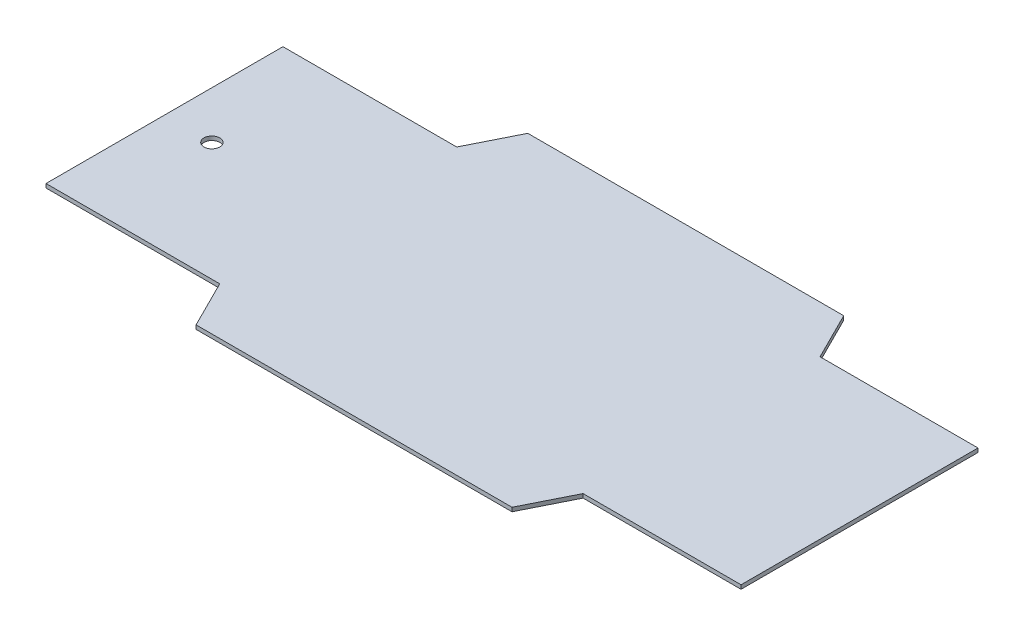
SolidWorks part; units mm, degrees
ref_plane "Front Plane" through (0, 0, 0) normal (0, 0, 1) x (1, 0, 0)
ref_plane "Top Plane" through (0, 0, 0) normal (0, 1, 0) x (1, 0, 0)
ref_plane "Right Plane" through (0, 0, 0) normal (1, 0, 0) x (0, 0, -1)
sketch "Sketch3" plane through (0, 0, 0) normal (0, 1, 0) x (1, 0, 0)
  line L0 (-279.4, 95.25) -> (-139.7, 95.25)
  line L1 (-279.4, -133.35) -> (279.4, -133.35) construction
  line L2 (-279.4, -133.35) -> (-279.4, 133.35) construction
  line L3 (-279.4, 133.35) -> (279.4, 133.35) construction
  line L4 (279.4, -133.35) -> (279.4, 133.35) construction
  line L5 (-279.4, -133.35) -> (279.4, 133.35) construction
  line L6 (-279.4, 133.35) -> (279.4, -133.35) construction
  line L7 (-279.4, -95.25) -> (279.4, -95.25) construction
  line L8 (-279.4, -95.25) -> (-279.4, 95.25) construction
  line L9 (-279.4, 95.25) -> (279.4, 95.25) construction
  line L10 (279.4, -95.25) -> (279.4, 95.25) construction
  line L13 (-139.7, 95.25) -> (-120.65, 133.35)
  line L14 (-120.65, 133.35) -> (133.35, 133.35)
  line L15 (133.35, 133.35) -> (152.4, 95.25)
  line L16 (152.4, 95.25) -> (279.4, 95.25)
  line L17 (-279.4, 95.25) -> (-279.4, -95.25)
  line L18 (279.4, 95.25) -> (279.4, -95.25)
  line L19 (-279.4, 0) -> (279.4, 0) construction
  line L20 (152.4, -95.25) -> (279.4, -95.25)
  line L21 (133.35, -133.35) -> (152.4, -95.25)
  line L22 (-120.65, -133.35) -> (133.35, -133.35)
  line L23 (-139.7, -95.25) -> (-120.65, -133.35)
  line L24 (-279.4, -95.25) -> (-139.7, -95.25)
  point P0 (0, 0)
  point P6 (0, 0)
  dimension "D1" = 266.7
  dimension "D2" = 558.8
  dimension "D3" = 190.5
  dimension "D4" = 127
  dimension "D5" = 139.7
  dimension "D6" = 254
extrude "Boss-Extrude1" add sketch "Sketch3" along normal mid plane 3.175
sketch "Sketch5" plane through (0, -1.5875, 0) normal (0, -1, 0) x (1, 0, 0)
  line L0 (-202.3532, 0) -> (279.4, 0) construction
  line L1 (-63.5, 25.4) -> (76.2, 25.4)
  line L2 (-63.5, 25.4) -> (-63.5, 88.9)
  line L3 (-63.5, 88.9) -> (76.2, 88.9)
  line L4 (76.2, 25.4) -> (76.2, 88.9)
  line L5 (-63.5, 25.4) -> (76.2, 88.9) construction
  line L6 (-63.5, 88.9) -> (76.2, 25.4) construction
  line L7 (279.4, 95.25) -> (279.4, -95.25) construction
  line L8 (-120.65, 133.35) -> (133.35, 133.35) construction
  line L9 (-120.65, 133.35) -> (133.35, 133.35) construction
  line L10 (6.35, 133.35) -> (6.35, 88.9) construction
  line L11 (-63.5, -88.9) -> (76.2, -88.9)
  line L12 (76.2, -25.4) -> (76.2, -88.9)
  line L13 (-63.5, -25.4) -> (76.2, -25.4)
  line L14 (-63.5, -25.4) -> (-63.5, -88.9)
  point P4 (6.35, 57.15)
  dimension "D1" = 63.5
  dimension "D2" = 139.7
  dimension "D3" = 44.45
sketch "Sketch6" plane through (0, 1.5875, 0) normal (0, 1, 0) x (1, 0, 0)
  line L0 (-279.4, 95.25) -> (-139.7, 95.25) construction
  line L1 (-120.65, 133.35) -> (-139.7, 95.25) construction
  line L2 (-139.7, 95.25) -> (-279.4, 95.25) construction
  line L3 (-139.7, 95.25) -> (-120.65, 133.35) construction
  line L4 (-120.65, 133.35) -> (133.35, 133.35) construction
  line L5 (133.35, 133.35) -> (152.4, 95.25) construction
  line L6 (152.4, 95.25) -> (279.4, 95.25) construction
  line L7 (279.4, 95.25) -> (279.4, -95.25) construction
  line L8 (279.4, -95.25) -> (152.4, -95.25) construction
  line L9 (133.35, -133.35) -> (152.4, -95.25) construction
  line L10 (152.4, -95.25) -> (279.4, -95.25) construction
  line L11 (152.4, -95.25) -> (133.35, -133.35) construction
  line L12 (133.35, -133.35) -> (-120.65, -133.35) construction
  line L13 (-120.65, -133.35) -> (-139.7, -95.25) construction
  line L14 (-139.7, -95.25) -> (-279.4, -95.25) construction
  line L15 (-279.4, -95.25) -> (-279.4, 95.25) construction
  line L16 (-276.225, 92.075) -> (-137.7377, 92.075)
  line L17 (-137.7377, 92.075) -> (-118.6877, 130.175)
  line L18 (-118.6877, 130.175) -> (131.3877, 130.175)
  line L19 (131.3877, 130.175) -> (150.4377, 92.075)
  line L20 (150.4377, 92.075) -> (276.225, 92.075)
  line L21 (276.225, 92.075) -> (276.225, -92.075)
  line L22 (276.225, -92.075) -> (150.4377, -92.075)
  line L23 (150.4377, -92.075) -> (131.3877, -130.175)
  line L24 (131.3877, -130.175) -> (-118.6877, -130.175)
  line L25 (-118.6877, -130.175) -> (-137.7377, -92.075)
  line L26 (-137.7377, -92.075) -> (-276.225, -92.075)
  line L27 (-276.225, -92.075) -> (-276.225, 92.075)
  dimension "D1" = 3.175
sketch "Sketch7" plane through (0, 1.5875, 0) normal (0, 1, 0) x (1, 0, 0)
  line L0 (-139.7, 95.25) -> (-139.7, -95.25) construction
  line L1 (-139.7, -95.25) -> (-279.4, -95.25) construction
  line L2 (-209.55, -95.25) -> (-209.55, 95.25) construction
  line L3 (-139.7, 95.25) -> (-279.4, 95.25) construction
  line L4 (-139.7, 0) -> (-279.4, 0) construction
  line L5 (-279.4, 95.25) -> (-279.4, -95.25) construction
  line L6 (-241.3, -66.675) -> (-177.8, -69.85) construction
  line L7 (-241.3, 69.85) -> (-177.8, 69.85)
  line L8 (-241.3, 69.85) -> (-241.3, 66.675)
  line L9 (-241.3, 66.675) -> (-177.8, 66.675)
  line L10 (-177.8, 69.85) -> (-177.8, 66.675)
  line L11 (-241.3, 69.85) -> (-177.8, 66.675) construction
  line L12 (-241.3, 66.675) -> (-177.8, 69.85) construction
  line L13 (-241.3, -69.85) -> (-177.8, -66.675) construction
  line L14 (-177.8, -69.85) -> (-177.8, -66.675)
  line L15 (-241.3, -66.675) -> (-177.8, -66.675)
  line L16 (-241.3, -69.85) -> (-241.3, -66.675)
  line L17 (-241.3, -69.85) -> (-177.8, -69.85)
  point P14 (-209.55, 68.2625)
  point P23 (-209.55, -68.2625)
  dimension "D1" = 3.175
  dimension "D2" = 63.5
  dimension "D3" = 25.4
sketch "Sketch8" plane through (0, 1.5875, 0) normal (0, 1, 0) x (1, 0, 0)
  line L0 (-139.7, 0) -> (-279.4, 0) construction
  line L1 (-241.3, 12.2856) -> (-241.3, -16.1319) construction
  line L3 (-241.3, -38.1) -> (-241.3, 38.1) construction
  circle A0 centre (-241.3, 0) radius 6.35
  point P4 (0, 0)
  dimension "D1" = 12.7
extrude "Cut-Extrude1" cut sketch "Sketch8" against normal blind 5.08
